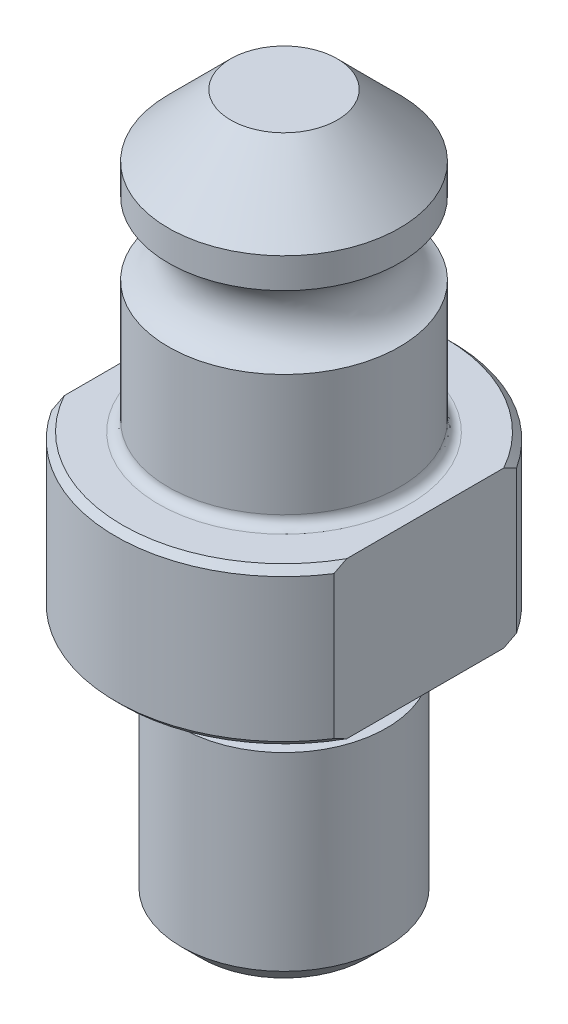
SolidWorks part; units mm, degrees
ref_plane "Front Plane" through (0, 0, 0) normal (0, 0, 1) x (1, 0, 0)
ref_plane "Top Plane" through (0, 0, 0) normal (0, 1, 0) x (1, 0, 0)
ref_plane "Right Plane" through (0, 0, 0) normal (1, 0, 0) x (0, 0, -1)
sketch "Sketch1" plane through (0, 0, 0) normal (0, 0, 1) x (1, 0, 0)
  line L0 (0, 35.0012) -> (0, -19.9898)
  line L1 (0, -19.9898) -> (-7.9375, -19.9898)
  line L2 (-7.9375, -19.9898) -> (-7.9375, -3.81)
  line L3 (-7.9375, -3.81) -> (-6.223, -3.81)
  line L4 (-6.223, -3.81) -> (-6.223, -1.27)
  line L5 (-7.493, 0) -> (-13.0048, 0)
  line L6 (-13.0048, 0) -> (-13.0048, 12.065)
  line L7 (-13.0048, 12.065) -> (-8.9408, 12.065)
  line L8 (-8.9408, 12.065) -> (-8.9408, 22.225)
  line L9 (-8.9408, 30.1752) -> (-4.1148, 35.0012)
  line L10 (-4.1148, 35.0012) -> (0, 35.0012)
  line L11 (0, -19.9898) -> (0, -73.6863) construction
  line L12 (-8.9408, 27.8384) -> (-8.9408, 30.1752)
  arc A0 (-8.9408, 22.225) -> (-8.9408, 27.8384) centre (-9.8817, 25.0317) ccw
  arc A1 (-7.493, 0) -> (-6.223, -1.27) centre (-7.493, -1.27) cw
  dimension "D13" = 13.843
  dimension "D14" = 1.27
  dimension "D1" = 15.875
  dimension "D2" = 12.446
  dimension "D3" = 26.0096
  dimension "D4" = 17.8816
  dimension "D5" = 19.9898
  dimension "D6" = 12.065
  dimension "D7" = 3.81
  dimension "D8" = 45
  dimension "D9" = 8.2296
  dimension "D10" = 35.0012
  dimension "D11" = 10.16
  dimension "D12" = 5.6134
revolve "Revolve1" add sketch "Sketch1" angle 360 about L11
chamfer "Chamfer1" distance 0.508 angle 45 2 edges at (-13.0048, 0, 0) (-13.0048, 12.065, 0)
chamfer "Chamfer2" distance 1.524 angle 45 1 edges at (-7.9375, -19.9898, 0)
sketch "Sketch2" plane through (0, 12.065, 0) normal (0, 1, 0) x (1, 0, 0)
  line L0 (-10.922, 7.0594) -> (-10.922, -7.0594)
  line L1 (10.922, 7.0594) -> (10.922, -7.0594)
  circle A0 centre (0, 0) radius 13.0048 construction
  arc A1 (10.922, -7.0594) -> (10.922, 7.0594) centre (0, 0) ccw
  arc A2 (-10.922, 7.0594) -> (-10.922, -7.0594) centre (0, 0) ccw
  dimension "D1" = 10.922
  dimension "D2" = 10.922
extrude "Cut-Extrude1" cut sketch "Sketch2" against normal through all
fillet "Fillet1" radius 0.762 1 edges at (-8.9408, 12.065, 0)
